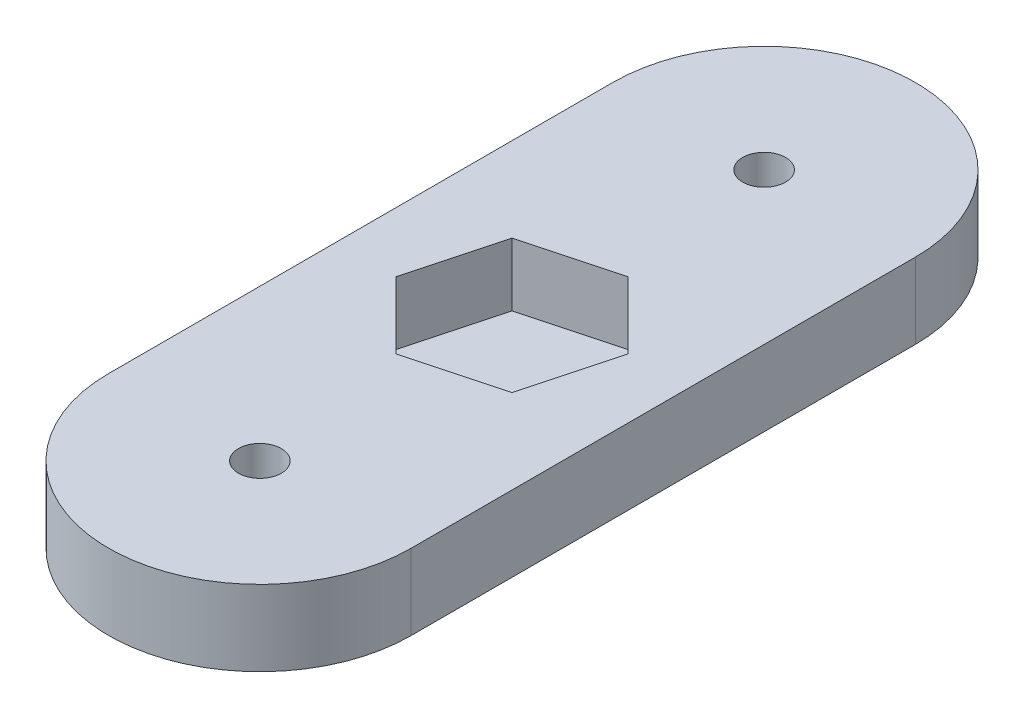
SolidWorks part; units mm, degrees
material "ABS PC"
ref_plane "Front Plane" through (0, 0, 0) normal (0, 0, 1) x (1, 0, 0)
ref_plane "Top Plane" through (0, 0, 0) normal (0, 1, 0) x (1, 0, 0)
ref_plane "Right Plane" through (0, 0, 0) normal (1, 0, 0) x (0, 0, -1)
sketch "Sketch1" plane through (0, 0, 0) normal (0, 1, 0) x (1, 0, 0)
  line L0 (0, 0) -> (0, 40) construction
  line L1 (-12, 0) -> (-12, 40)
  line L2 (12, 0) -> (12, 40)
  arc A0 (-12, 0) -> (12, 0) centre (0, 0) ccw
  arc A1 (12, 40) -> (-12, 40) centre (0, 40) ccw
  circle A2 centre (0, 40) radius 1.7
  circle A3 centre (0, 0) radius 1.7
  point P3 (0, 20)
  dimension "D2" = 40
  dimension "D3" = 3.4
  dimension "D1" = 24
extrude "Boss-Extrude1" add sketch "Sketch1" along normal blind 6
sketch "Sketch2" plane through (0, 6, 0) normal (0, 1, 0) x (1, 0, 0)
  line L0 (12, 0) -> (12, 40) construction
  line L1 (5.3072, 14.6928) -> (7.2498, 21.9426)
  line L2 (7.2498, 21.9426) -> (1.9426, 27.2498)
  line L3 (1.9426, 27.2498) -> (-5.3072, 25.3072)
  line L4 (-5.3072, 25.3072) -> (-7.2498, 18.0574)
  line L5 (-7.2498, 18.0574) -> (-1.9426, 12.7502)
  line L6 (-1.9426, 12.7502) -> (5.3072, 14.6928)
  line L7 (-12, 40) -> (-12, 0) construction
  circle A0 centre (0, 20) radius 6.5 construction
  dimension "D1" = 13
  dimension "D2" = 12
  dimension "D3" = 20
  dimension "D4" = 105
extrude "Cut-Extrude1" cut sketch "Sketch2" against normal blind 5
